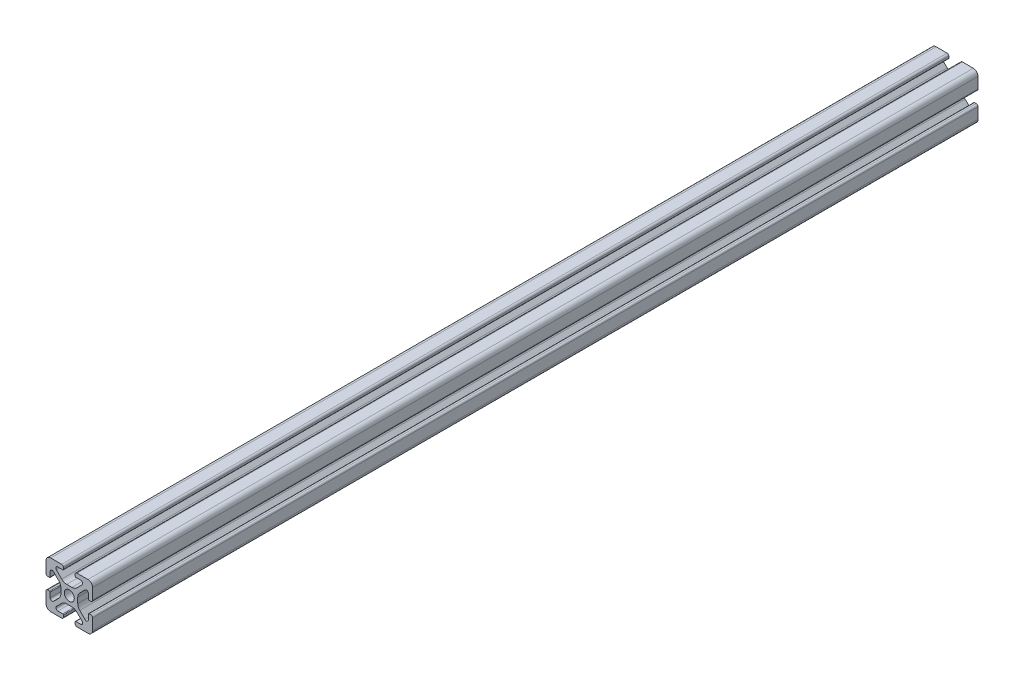
SolidWorks part; units mm, degrees
material "6061-T6 (SS)"
ref_plane "Front Plane" through (0, 0, 0) normal (0, 0, 1) x (1, 0, 0)
ref_plane "Top Plane" through (0, 0, 0) normal (0, 1, 0) x (1, 0, 0)
ref_plane "Right Plane" through (0, 0, 0) normal (1, 0, 0) x (0, 0, -1)
sketch "Sketch1" plane through (0, 0, 0) normal (0, 0, 1) x (1, 0, 0)
  line L2 (-9.9949, 7.9883) -> (-9.9949, 3.2893)
  line L3 (-7.9883, 9.9949) -> (-3.2893, 9.9949)
  line L4 (-2.5019, 9.2075) -> (-2.5019, 8.4963)
  line L5 (-2.8067, 8.1915) -> (-4.9149, 8.1915)
  line L6 (-5.5076, 6.7606) -> (-3.2528, 4.5058)
  line L7 (-6.7606, 5.5076) -> (-4.5058, 3.2528)
  line L8 (-8.1915, 4.9149) -> (-8.1915, 2.8067)
  line L9 (-8.4963, 2.5019) -> (-9.2075, 2.5019)
  line L11 (-1.1334, 3.6279) -> (1.1334, 3.6279)
  line L12 (-3.6279, 1.1334) -> (-3.6279, -1.1334)
  line L13 (8.4963, 2.5019) -> (9.2075, 2.5019)
  line L14 (8.1915, 4.9149) -> (8.1915, 2.8067)
  line L15 (9.9949, 7.9883) -> (9.9949, 3.2893)
  line L16 (7.9883, 9.9949) -> (3.2893, 9.9949)
  line L17 (2.5019, 9.2075) -> (2.5019, 8.4963)
  line L18 (2.8067, 8.1915) -> (4.9149, 8.1915)
  line L19 (3.6279, 1.1334) -> (3.6279, -1.1334)
  line L20 (5.5076, 6.7606) -> (3.2528, 4.5058)
  line L21 (6.7606, 5.5076) -> (4.5058, 3.2528)
  line L22 (-8.4963, -2.5019) -> (-9.2075, -2.5019)
  line L23 (-8.1915, -4.9149) -> (-8.1915, -2.8067)
  line L24 (-6.7606, -5.5076) -> (-4.5058, -3.2528)
  line L25 (-5.5076, -6.7606) -> (-3.2528, -4.5058)
  line L26 (-2.8067, -8.1915) -> (-4.9149, -8.1915)
  line L27 (-2.5019, -9.2075) -> (-2.5019, -8.4963)
  line L28 (-7.9883, -9.9949) -> (-3.2893, -9.9949)
  line L29 (-9.9949, -7.9883) -> (-9.9949, -3.2893)
  line L30 (9.9949, -7.9883) -> (9.9949, -3.2893)
  line L31 (7.9883, -9.9949) -> (3.2893, -9.9949)
  line L32 (2.5019, -9.2075) -> (2.5019, -8.4963)
  line L33 (2.8067, -8.1915) -> (4.9149, -8.1915)
  line L34 (5.5076, -6.7606) -> (3.2528, -4.5058)
  line L35 (6.7606, -5.5076) -> (4.5058, -3.2528)
  line L36 (8.1915, -4.9149) -> (8.1915, -2.8067)
  line L37 (8.4963, -2.5019) -> (9.2075, -2.5019)
  line L38 (-1.1334, -3.6279) -> (1.1334, -3.6279)
  circle A0 centre (0, 0) radius 2.1463
  arc A1 (-9.9949, 7.9883) -> (-7.9883, 9.9949) centre (-7.9883, 7.9883) cw
  arc A2 (-6.7606, 5.5076) -> (-8.1915, 4.9149) centre (-7.3533, 4.9149) ccw
  arc A3 (-4.9149, 8.1915) -> (-5.5076, 6.7606) centre (-4.9149, 7.3533) ccw
  arc A4 (-3.2893, 9.9949) -> (-2.5019, 9.2075) centre (-3.2893, 9.2075) cw
  arc A5 (-9.9949, 3.2893) -> (-9.2075, 2.5019) centre (-9.2075, 3.2893) ccw
  arc A6 (-8.1915, 2.8067) -> (-8.4963, 2.5019) centre (-8.4963, 2.8067) cw
  arc A7 (-2.5019, 8.4963) -> (-2.8067, 8.1915) centre (-2.8067, 8.4963) cw
  arc A8 (-1.1334, 3.6279) -> (-3.2528, 4.5058) centre (-1.1334, 6.6251) cw
  arc A9 (-3.6279, 1.1334) -> (-4.5058, 3.2528) centre (-6.6251, 1.1334) ccw
  arc A10 (8.1915, 2.8067) -> (8.4963, 2.5019) centre (8.4963, 2.8067) ccw
  arc A11 (9.9949, 3.2893) -> (9.2075, 2.5019) centre (9.2075, 3.2893) cw
  arc A12 (9.9949, 7.9883) -> (7.9883, 9.9949) centre (7.9883, 7.9883) ccw
  arc A13 (3.2893, 9.9949) -> (2.5019, 9.2075) centre (3.2893, 9.2075) ccw
  arc A14 (2.5019, 8.4963) -> (2.8067, 8.1915) centre (2.8067, 8.4963) ccw
  arc A15 (1.1334, 3.6279) -> (3.2528, 4.5058) centre (1.1334, 6.6251) ccw
  arc A16 (3.6279, 1.1334) -> (4.5058, 3.2528) centre (6.6251, 1.1334) cw
  arc A17 (6.7606, 5.5076) -> (8.1915, 4.9149) centre (7.3533, 4.9149) cw
  arc A18 (4.9149, 8.1915) -> (5.5076, 6.7606) centre (4.9149, 7.3533) cw
  arc A19 (-3.6279, -1.1334) -> (-4.5058, -3.2528) centre (-6.6251, -1.1334) cw
  arc A20 (-1.1334, -3.6279) -> (-3.2528, -4.5058) centre (-1.1334, -6.6251) ccw
  arc A21 (-2.5019, -8.4963) -> (-2.8067, -8.1915) centre (-2.8067, -8.4963) ccw
  arc A22 (-8.1915, -2.8067) -> (-8.4963, -2.5019) centre (-8.4963, -2.8067) ccw
  arc A23 (-9.9949, -3.2893) -> (-9.2075, -2.5019) centre (-9.2075, -3.2893) cw
  arc A24 (-3.2893, -9.9949) -> (-2.5019, -9.2075) centre (-3.2893, -9.2075) ccw
  arc A25 (-4.9149, -8.1915) -> (-5.5076, -6.7606) centre (-4.9149, -7.3533) cw
  arc A26 (-6.7606, -5.5076) -> (-8.1915, -4.9149) centre (-7.3533, -4.9149) cw
  arc A27 (-9.9949, -7.9883) -> (-7.9883, -9.9949) centre (-7.9883, -7.9883) ccw
  arc A28 (9.9949, -7.9883) -> (7.9883, -9.9949) centre (7.9883, -7.9883) cw
  arc A29 (6.7606, -5.5076) -> (8.1915, -4.9149) centre (7.3533, -4.9149) ccw
  arc A30 (4.9149, -8.1915) -> (5.5076, -6.7606) centre (4.9149, -7.3533) ccw
  arc A31 (3.2893, -9.9949) -> (2.5019, -9.2075) centre (3.2893, -9.2075) cw
  arc A32 (9.9949, -3.2893) -> (9.2075, -2.5019) centre (9.2075, -3.2893) ccw
  arc A33 (8.1915, -2.8067) -> (8.4963, -2.5019) centre (8.4963, -2.8067) cw
  arc A34 (2.5019, -8.4963) -> (2.8067, -8.1915) centre (2.8067, -8.4963) cw
  arc A35 (1.1334, -3.6279) -> (3.2528, -4.5058) centre (1.1334, -6.6251) cw
  arc A36 (3.6279, -1.1334) -> (4.5058, -3.2528) centre (6.6251, -1.1334) ccw
extrude "Boss-Extrude1" add sketch "Sketch1" along normal blind 380.0204
